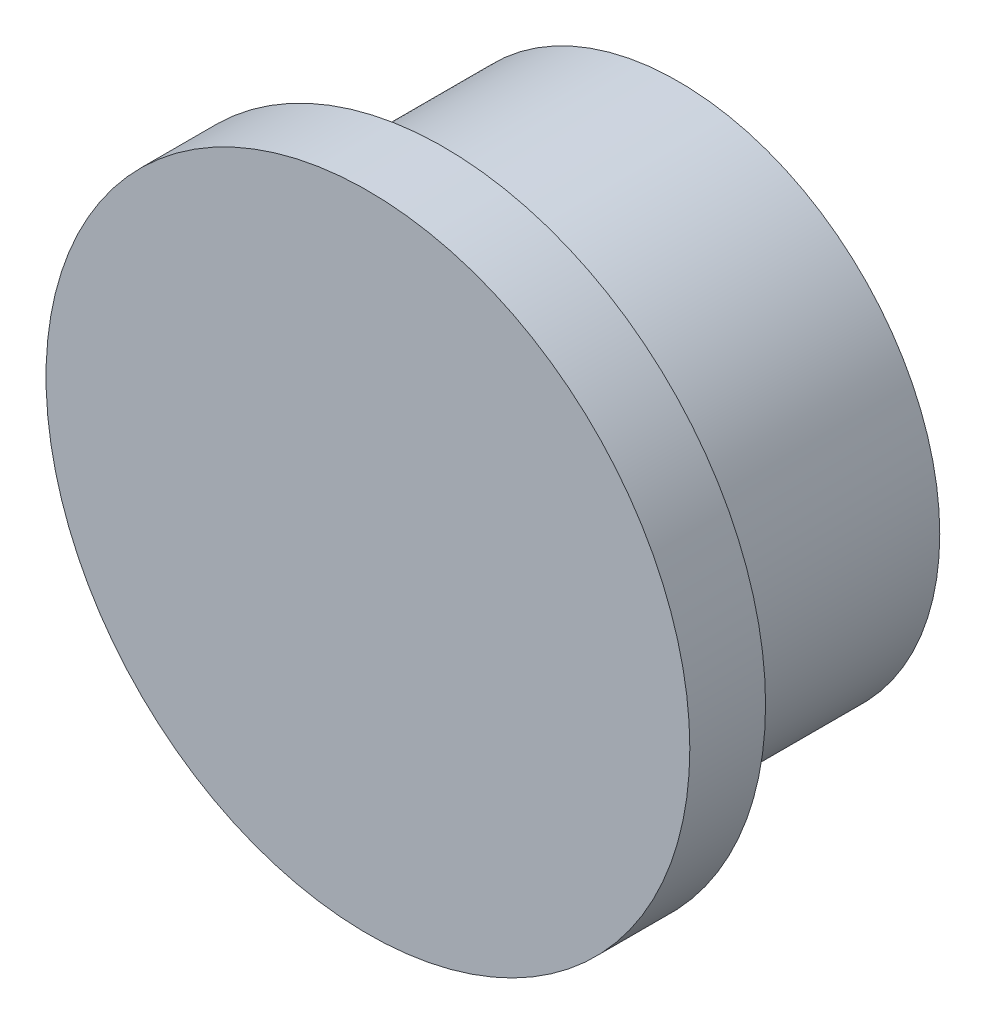
SolidWorks part; units mm, degrees
ref_plane "Alzado" through (0, 0, 0) normal (0, 0, 1) x (1, 0, 0)
ref_plane "Planta" through (0, 0, 0) normal (0, 1, 0) x (1, 0, 0)
ref_plane "Vista lateral" through (0, 0, 0) normal (1, 0, 0) x (0, 0, -1)
sketch "Croquis1" plane through (0, 0, 0) normal (0, 0, 1) x (1, 0, 0)
  circle A0 centre (0, 0) radius 3.45
  circle A1 centre (0, 0) radius 2.45
  dimension "D1" = 4.9
  dimension "D2" = 1
extrude "Saliente-Extruir1" add sketch "Croquis1" along normal blind 3.1
sketch "Croquis2" plane through (0, 0, 3.1) normal (0, 0, 1) x (1, 0, 0)
  circle A0 centre (0, 0) radius 4.25
  dimension "D1" = 8.5
extrude "Saliente-Extruir2" add sketch "Croquis2" along normal blind 1
